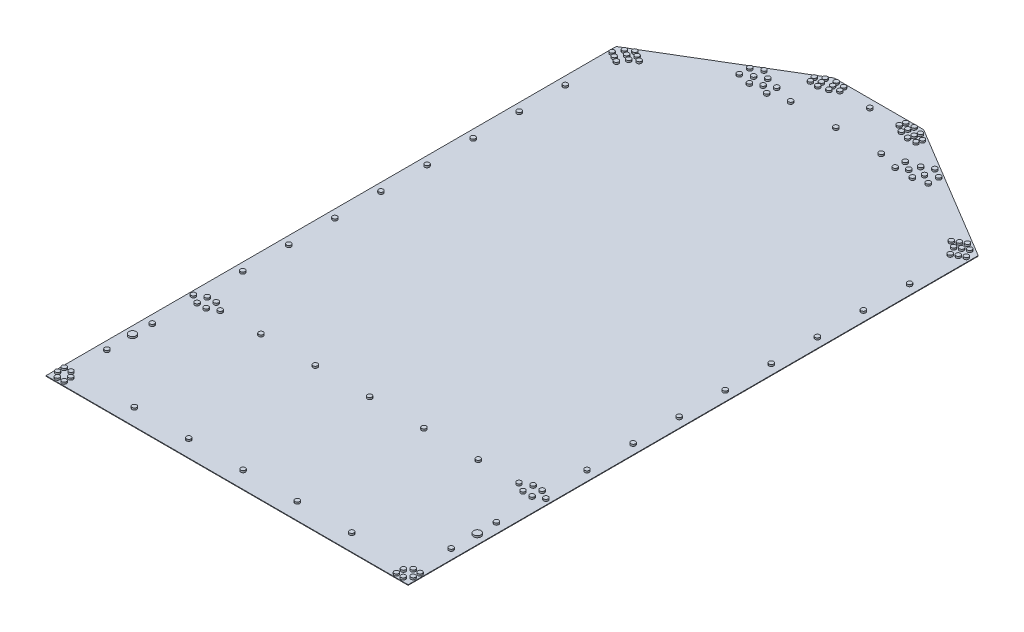
SolidWorks part; units mm, degrees
material "6061-T6 (SS)"
ref_plane "Front Plane" through (0, 0, 0) normal (0, 0, 1) x (1, 0, 0)
ref_plane "Top Plane" through (0, 0, 0) normal (0, 1, 0) x (1, 0, 0)
ref_plane "Right Plane" through (0, 0, 0) normal (1, 0, 0) x (0, 0, -1)
sketch "Sketch1" plane through (0, 0, 0) normal (0, 1, 0) x (1, 0, 0)
  line L0 (-125.4125, 0) -> (125.4125, 0)
  line L1 (-125.4125, 0) -> (-508, -229.4171)
  line L2 (125.4125, 0) -> (508, -229.4171)
  line L3 (-508, -229.4171) -> (-508, -1828.8)
  line L4 (-508, -1828.8) -> (508, -1828.8)
  line L5 (508, -1828.8) -> (508, -229.4171)
  point P3 (0, 0)
  point P4 (0, -1828.8)
  dimension "D1" = 250.825
  dimension "D2" = 446.1002
  dimension "D3" = 446.1002
  dimension "D4" = 1828.8
  dimension "D5" = 1016
extrude "Boss-Extrude1" add sketch "Sketch1" along normal blind 1.6256
sketch "Sketch2" plane through (0, 1.6256, 0) normal (0, 1, 0) x (1, 0, 0)
  line L0 (-508, -1828.8) -> (508, -1828.8) construction
  line L1 (-508, -229.4171) -> (-508, -1828.8) construction
  line L2 (508, -1828.8) -> (508, -229.4171) construction
  line L3 (444.5, -1414.7546) -> (444.5, -1443.0502) construction
  line L4 (-469.9, -1414.7546) -> (-469.9, -1443.0502) construction
  line L5 (0, 0) -> (0, -1828.8) construction
  line L6 (482.7037, -259.9683) -> (470.0037, -237.9712) construction
  line L7 (468.4056, -268.2233) -> (497.0018, -251.7133) construction
  line L8 (508, -229.4171) -> (125.4125, 0) construction
  line L9 (482.7037, -259.9683) -> (482.7037, -214.2483) construction
  line L10 (455.7056, -246.2262) -> (484.3018, -229.7162) construction
  line L11 (437.9453, -234.6591) -> (466.5414, -218.1491) construction
  line L12 (478.0899, -211.4816) -> (466.5414, -218.1491) construction
  line L13 (-180.2733, -106.68) -> (-234.232, -137.8331) construction
  line L14 (-239.7213, -111.887) -> (-239.7213, -82.677) construction
  line L15 (-214.4247, -97.282) -> (-239.7213, -111.887) construction
  line L16 (125.4125, 0) -> (-125.4125, 0) construction
  line L17 (204.47, -120.65) -> (180.2733, -106.68) construction
  line L18 (180.2733, -106.68) -> (180.2733, -134.62) construction
  line L19 (180.2733, -134.62) -> (204.47, -120.65) construction
  line L20 (-239.7213, -82.677) -> (-214.4247, -97.282) construction
  line L21 (239.7213, -82.677) -> (214.4247, -97.282) construction
  line L22 (214.4247, -97.282) -> (239.7213, -111.887) construction
  line L23 (239.7213, -111.887) -> (239.7213, -82.677) construction
  line L24 (180.2733, -106.68) -> (234.232, -137.8331) construction
  line L25 (-180.2733, -134.62) -> (-204.47, -120.65) construction
  line L26 (-180.2733, -106.68) -> (-180.2733, -134.62) construction
  line L27 (-204.47, -120.65) -> (-180.2733, -106.68) construction
  line L28 (-478.0899, -211.4816) -> (-466.5414, -218.1491) construction
  line L29 (-437.9453, -234.6591) -> (-466.5414, -218.1491) construction
  line L30 (-455.7056, -246.2262) -> (-484.3018, -229.7162) construction
  line L31 (-482.7037, -259.9683) -> (-482.7037, -214.2483) construction
  line L32 (-468.4056, -268.2233) -> (-497.0018, -251.7133) construction
  line L33 (-482.7037, -259.9683) -> (-470.0037, -237.9712) construction
  line L34 (125.4125, 0) -> (106.2386, -69.2587) construction
  line L35 (85.3596, -19.0136) -> (149.9848, -36.9046) construction
  line L36 (133.8085, -17.272) -> (126.0151, -45.4231) construction
  line L37 (148.0195, -44.0036) -> (151.9501, -29.8057) construction
  line L38 (-148.0195, -44.0036) -> (-151.9501, -29.8057) construction
  line L39 (-133.8085, -17.272) -> (-126.0151, -45.4231) construction
  line L40 (-85.3596, -19.0136) -> (-149.9848, -36.9046) construction
  circle A0 centre (-304.8, -1783.9436) radius 6.4262
  circle A1 centre (-152.4, -1783.9436) radius 6.4262
  circle A2 centre (0, -1783.9436) radius 6.4262
  circle A3 centre (152.4, -1783.9436) radius 6.4262
  circle A4 centre (304.8, -1783.9436) radius 6.4262
  circle A5 centre (-304.8, -1428.9024) radius 6.4262
  circle A6 centre (-152.4, -1428.9024) radius 6.4262
  circle A7 centre (0, -1428.9024) radius 6.4262
  circle A8 centre (152.4, -1428.9024) radius 6.4262
  circle A9 centre (304.8, -1428.9024) radius 6.4262
  circle A10 centre (-482.9048, -1301.9024) radius 6.4262
  circle A11 centre (-482.9048, -1172.6418) radius 6.4262
  circle A12 centre (-482.9048, -1043.3812) radius 6.4262
  circle A13 centre (-482.9048, -914.1206) radius 6.4262
  circle A14 centre (-482.9048, -784.86) radius 6.4262
  circle A15 centre (-482.9048, -655.5994) radius 6.4262
  circle A16 centre (-482.9048, -526.3388) radius 6.4262
  circle A17 centre (-482.9048, -397.0782) radius 6.4262
  circle A18 centre (482.9048, -1301.9024) radius 6.4262
  circle A19 centre (482.9048, -1172.6418) radius 6.4262
  circle A20 centre (482.9048, -1043.3812) radius 6.4262
  circle A21 centre (482.9048, -914.1206) radius 6.4262
  circle A22 centre (482.9048, -784.86) radius 6.4262
  circle A23 centre (482.9048, -655.5994) radius 6.4262
  circle A24 centre (482.9048, -526.3388) radius 6.4262
  circle A25 centre (482.9048, -397.0782) radius 6.4262
  circle A26 centre (444.5, -1414.7546) radius 6.4262
  circle A27 centre (469.9, -1414.7546) radius 6.4262
  circle A28 centre (444.5, -1443.0502) radius 6.4262
  circle A29 centre (469.9, -1443.0502) radius 6.4262
  circle A30 centre (-469.9, -1414.7546) radius 6.4262
  circle A31 centre (-444.5, -1414.7546) radius 6.4262
  circle A32 centre (-469.9, -1443.0502) radius 6.4262
  circle A33 centre (-444.5, -1443.0502) radius 6.4262
  circle A34 centre (419.1, -1428.9024) radius 6.4262
  circle A35 centre (0, -25.4) radius 6.4262
  circle A36 centre (494.411, -1428.9024) radius 6.4262
  circle A37 centre (-494.411, -1428.9024) radius 6.4262
  circle A38 centre (-419.1, -1428.9024) radius 6.4262
  circle A39 centre (466.09, -1819.783) radius 6.4262
  circle A40 centre (466.852, -1800.7838) radius 6.4262
  circle A41 centre (485.14, -1819.783) radius 6.4262
  circle A42 centre (498.729, -1805.6352) radius 6.4262
  circle A43 centre (480.06, -1786.5852) radius 6.4262
  circle A44 centre (499.11, -1786.5852) radius 6.4262
  circle A45 centre (-466.852, -1800.7838) radius 6.4262
  circle A46 centre (-466.09, -1819.783) radius 6.4262
  circle A47 centre (-485.14, -1819.783) radius 6.4262
  circle A48 centre (-498.729, -1805.6352) radius 6.4262
  circle A49 centre (-499.11, -1786.5852) radius 6.4262
  circle A50 centre (-480.06, -1786.5852) radius 6.4262
  circle A51 centre (482.9048, -1555.9024) radius 6.4262
  circle A52 centre (482.9048, -1682.9024) radius 6.4262
  circle A53 centre (-482.9048, -1682.9024) radius 6.4262
  circle A54 centre (-482.9048, -1555.9024) radius 6.4262
  circle A55 centre (468.4056, -268.2233) radius 6.4262
  circle A56 centre (482.7037, -259.9683) radius 6.4262
  circle A57 centre (497.0018, -251.7133) radius 6.4262
  circle A58 centre (455.7056, -246.2262) radius 6.4262
  circle A59 centre (470.0037, -237.9712) radius 6.4262
  circle A60 centre (484.3018, -229.7162) radius 6.4262
  circle A61 centre (437.9453, -234.6591) radius 6.4262
  circle A62 centre (452.2434, -226.4041) radius 6.4262
  circle A63 centre (466.5414, -218.1491) radius 6.4262
  circle A64 centre (-228.6667, -134.62) radius 6.4262
  circle A65 centre (-265.0179, -126.492) radius 6.4262
  circle A66 centre (-265.0179, -97.282) radius 6.4262
  circle A67 centre (-239.7213, -111.887) radius 6.4262
  circle A68 centre (-239.7213, -82.677) radius 6.4262
  circle A69 centre (-214.4247, -97.282) radius 6.4262
  circle A70 centre (-180.2733, -134.62) radius 6.4262
  circle A71 centre (-180.2733, -106.68) radius 6.4262
  circle A72 centre (-204.47, -120.65) radius 6.4262
  circle A73 centre (0, -120.65) radius 6.4262
  circle A74 centre (-127, -120.65) radius 6.4262
  circle A75 centre (127, -120.65) radius 6.4262
  circle A76 centre (204.47, -120.65) radius 6.4262
  circle A77 centre (180.2733, -106.68) radius 6.4262
  circle A78 centre (180.2733, -134.62) radius 6.4262
  circle A79 centre (214.4247, -97.282) radius 6.4262
  circle A80 centre (239.7213, -82.677) radius 6.4262
  circle A81 centre (239.7213, -111.887) radius 6.4262
  circle A82 centre (265.0179, -97.282) radius 6.4262
  circle A83 centre (265.0179, -126.492) radius 6.4262
  circle A84 centre (228.6667, -134.62) radius 6.4262
  circle A85 centre (-466.5414, -218.1491) radius 6.4262
  circle A86 centre (-452.2434, -226.4041) radius 6.4262
  circle A87 centre (-437.9453, -234.6591) radius 6.4262
  circle A88 centre (-484.3018, -229.7162) radius 6.4262
  circle A89 centre (-470.0037, -237.9712) radius 6.4262
  circle A90 centre (-455.7056, -246.2262) radius 6.4262
  circle A91 centre (-497.0018, -251.7133) radius 6.4262
  circle A92 centre (-482.7037, -259.9683) radius 6.4262
  circle A93 centre (-468.4056, -268.2233) radius 6.4262
  circle A94 centre (129.9118, -31.3476) radius 6.4262
  circle A95 centre (133.8085, -17.272) radius 6.4262
  circle A96 centre (126.0151, -45.4231) radius 6.4262
  circle A97 centre (151.9501, -29.8057) radius 6.4262
  circle A98 centre (148.0195, -44.0036) radius 6.4262
  circle A99 centre (83.3943, -26.1125) radius 6.4262
  circle A100 centre (87.3249, -11.9146) radius 6.4262
  circle A101 centre (105.4326, -24.5706) radius 6.4262
  circle A102 centre (101.5358, -38.6462) radius 6.4262
  circle A103 centre (109.3293, -10.4951) radius 6.4262
  circle A104 centre (-109.3293, -10.4951) radius 6.4262
  circle A105 centre (-101.5358, -38.6462) radius 6.4262
  circle A106 centre (-105.4326, -24.5706) radius 6.4262
  circle A107 centre (-87.3249, -11.9146) radius 6.4262
  circle A108 centre (-83.3943, -26.1125) radius 6.4262
  circle A109 centre (-148.0195, -44.0036) radius 6.4262
  circle A110 centre (-151.9501, -29.8057) radius 6.4262
  circle A111 centre (-126.0151, -45.4231) radius 6.4262
  circle A112 centre (-133.8085, -17.272) radius 6.4262
  circle A113 centre (-129.9118, -31.3476) radius 6.4262
  circle A114 centre (483.743, -1610.487) radius 10.287
  circle A115 centre (-483.743, -1610.487) radius 10.287
  point P66 (444.5, -1428.9024)
  point P75 (-469.9, -1428.9024)
  point P219 (117.6722, -27.9591)
  dimension "D1" = 12.8524
  dimension "D2" = 12.8524
  dimension "D3" = 12.8524
  dimension "D4" = 12.8524
  dimension "D5" = 12.8524
  dimension "D6" = 44.8564
  dimension "D13" = 12.8524
  dimension "D14" = 12.8524
  dimension "D15" = 12.8524
  dimension "D16" = 12.8524
  dimension "D17" = 12.8524
  dimension "D24" = 12.8524
  dimension "D25" = 12.8524
  dimension "D26" = 12.8524
  dimension "D27" = 12.8524
  dimension "D28" = 12.8524
  dimension "D29" = 12.8524
  dimension "D30" = 12.8524
  dimension "D31" = 12.8524
  dimension "D32" = 526.8976
  dimension "D41" = 12.8524
  dimension "D42" = 12.8524
  dimension "D43" = 12.8524
  dimension "D44" = 12.8524
  dimension "D45" = 12.8524
  dimension "D46" = 12.8524
  dimension "D47" = 12.8524
  dimension "D48" = 12.8524
  dimension "D58" = 12.8524
  dimension "D59" = 12.8524
  dimension "D60" = 12.8524
  dimension "D61" = 12.8524
  dimension "D65" = 12.8524
  dimension "D66" = 12.8524
  dimension "D67" = 12.8524
  dimension "D71" = 12.8524
  dimension "D72" = 12.8524
  dimension "D74" = 95.25
  dimension "D75" = 12.8524
  dimension "D76" = 75.311
  dimension "D77" = 12.8524
  dimension "D78" = 12.8524
  dimension "D81" = 12.8524
  dimension "D82" = 12.8524
  dimension "D83" = 12.8524
  dimension "D89" = 12.8524
  dimension "D90" = 12.8524
  dimension "D91" = 12.8524
  dimension "D97" = 12.8524
  dimension "D98" = 12.8524
  dimension "D102" = 12.8524
  dimension "D103" = 12.8524
  dimension "D104" = 12.8524
  dimension "D109" = 12.8524
  dimension "D110" = 12.8524
  dimension "D111" = 12.8524
  dimension "D115" = 12.8524
  dimension "D116" = 12.8524
  dimension "D117" = 12.8524
  dimension "D123" = 12.8524
  dimension "D124" = 12.8524
  dimension "D125" = 12.8524
  dimension "D126" = 12.8524
  dimension "D129" = 12.8524
  dimension "D133" = 12.8524
  dimension "D134" = 12.8524
  dimension "D135" = 12.8524
  dimension "D141" = 12.8524
  dimension "D142" = 12.8524
  dimension "D143" = 12.8524
  dimension "D146" = 12.8524
  dimension "D148" = 12.8524
  dimension "D150" = 27.94
  dimension "D152" = 12.8524
  dimension "D153" = 12.8524
  dimension "D156" = 12.8524
  dimension "D158" = 12.8524
  dimension "D159" = 12.8524
  dimension "D162" = 20.574
  dimension "D7" = 203.2
  dimension "D8" = 152.4
  dimension "D9" = 152.4
  dimension "D10" = 152.4
  dimension "D11" = 152.4
  dimension "D12" = 203.2
  dimension "D18" = 152.4
  dimension "D19" = 152.4
  dimension "D20" = 152.4
  dimension "D21" = 152.4
  dimension "D22" = 203.2
  dimension "D23" = 399.8976
  dimension "D33" = 25.0952
  dimension "D34" = 129.2606
  dimension "D35" = 129.2606
  dimension "D36" = 129.2606
  dimension "D37" = 129.2606
  dimension "D38" = 129.2606
  dimension "D39" = 129.2606
  dimension "D40" = 129.2606
  dimension "D49" = 129.2606
  dimension "D50" = 129.2606
  dimension "D51" = 129.2606
  dimension "D52" = 129.2606
  dimension "D53" = 129.2606
  dimension "D54" = 129.2606
  dimension "D55" = 129.2606
  dimension "D56" = 25.0952
  dimension "D57" = 526.8976
  dimension "D62" = 28.2956
  dimension "D63" = 25.4
  dimension "D64" = 38.1
  dimension "D68" = 28.2956
  dimension "D69" = 25.4
  dimension "D70" = 38.1
  dimension "D73" = 114.3
  dimension "D79" = 114.3
  dimension "D80" = 75.311
  dimension "D84" = 19.05
  dimension "D85" = 9.017
  dimension "D86" = 22.86
  dimension "D87" = 28.0162
  dimension "D88" = 41.148
  dimension "D92" = 19.05
  dimension "D93" = 8.89
  dimension "D94" = 42.2148
  dimension "D95" = 9.271
  dimension "D96" = 23.1648
  dimension "D99" = 127
  dimension "D100" = 254
  dimension "D101" = 60
  dimension "D105" = 16.51
  dimension "D106" = 33.02
  dimension "D107" = 10.9982
  dimension "D108" = 45.72
  dimension "D112" = 25.4
  dimension "D113" = 16.51
  dimension "D114" = 33.02
  dimension "D118" = 16.51
  dimension "D119" = 33.02
  dimension "D120" = 13.335
  dimension "D121" = 18.8976
  dimension "D122" = 25.4
  dimension "D127" = 127
  dimension "D128" = 127
  dimension "D130" = 77.47
  dimension "D131" = 60
  dimension "D132" = 27.94
  dimension "D136" = 25.4
  dimension "D137" = 23.368
  dimension "D138" = 29.21
  dimension "D139" = 29.21
  dimension "D140" = 60
  dimension "D144" = 29.21
  dimension "D145" = 29.21
  dimension "D147" = 29.21
  dimension "D149" = 27.94
  dimension "D151" = 67.056
  dimension "D154" = 12.7
  dimension "D155" = 29.21
  dimension "D157" = 14.732
  dimension "D160" = 17.272
  dimension "D161" = 69.2587
  dimension "D163" = 24.257
  dimension "D164" = 218.313
fillet "Fillet1" radius 4.191 2 edges at (-508, 0.8128, 229.4171) (508, 0.8128, 229.4171)
fillet "Fillet2" radius 4.191 2 edges at (-125.4125, 0.8128, 0) (125.4125, 0.8128, 0)
extrude "Boss-Extrude2" add sketch "Sketch2" along normal blind 5.08
